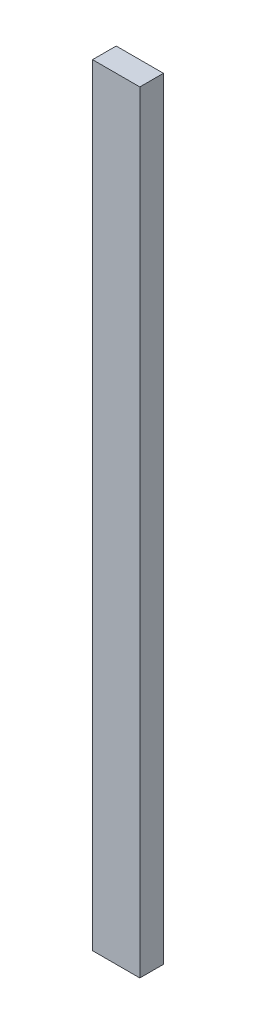
SolidWorks part; units mm, degrees
ref_plane "Plane1" through (0, 0, 0) normal (0, 0, 1) x (1, 0, 0)
ref_plane "Plane2" through (0, 0, 0) normal (0, 1, 0) x (1, 0, 0)
ref_plane "Plane3" through (0, 0, 0) normal (1, 0, 0) x (0, 0, -1)
sketch "Sketch1" plane through (0, 0, 0) normal (0, 1, 0) x (1, 0, 0)
  line L1 (0, 0) -> (30, 0)
  line L2 (0, 0) -> (0, 15)
  line L3 (0, 15) -> (30, 15)
  line L4 (30, 0) -> (30, 15)
  dimension "D1" = 30
  dimension "D2" = 15
extrude "Boss-Extrude1" add sketch "Sketch1" along normal blind 490
